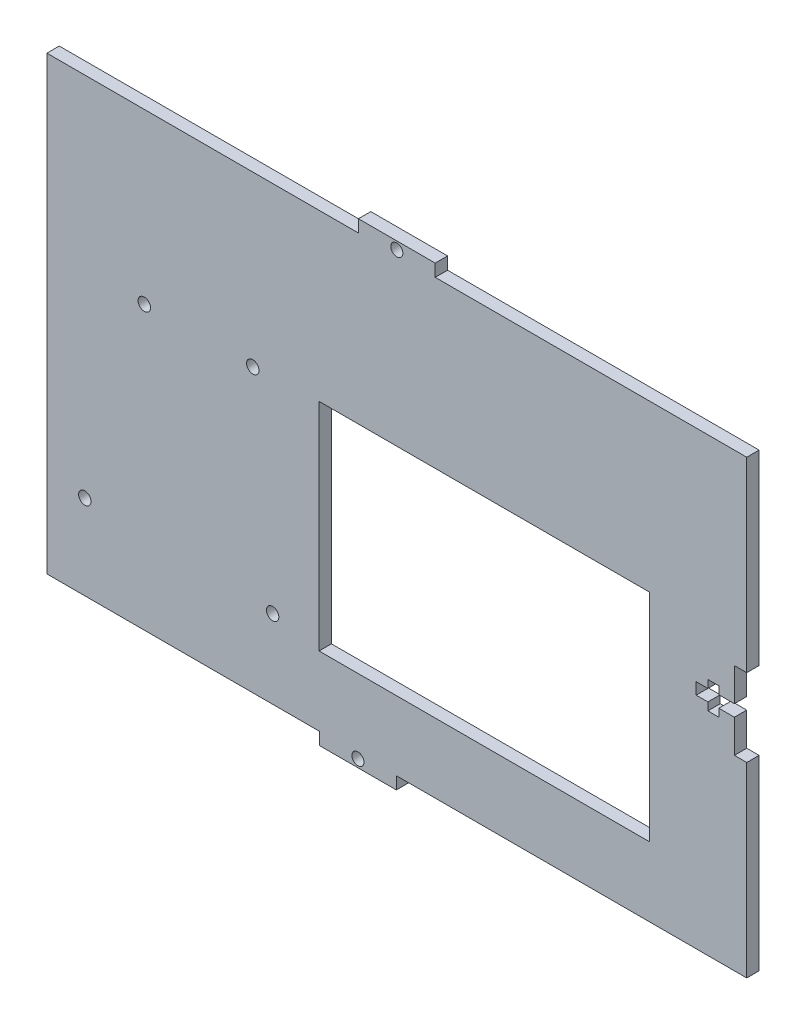
SolidWorks part; units mm, degrees
ref_plane "Front Plane" through (0, 0, 0) normal (0, 0, 1) x (1, 0, 0)
ref_plane "Top Plane" through (0, 0, 0) normal (0, 1, 0) x (1, 0, 0)
ref_plane "Right Plane" through (0, 0, 0) normal (1, 0, 0) x (0, 0, -1)
sketch "Sketch1" plane through (0, 0, 0) normal (0, 0, 1) x (1, 0, 0)
  line L1 (-90, 61.18) -> (90, 61.18)
  line L2 (-90, 61.18) -> (-90, -61.18)
  line L3 (-90, -61.18) -> (90, -61.18)
  line L4 (90, 61.18) -> (90, -61.18)
  dimension "D1" = 61.18
  dimension "D2" = 122.36
  dimension "D3" = 180
  dimension "D4" = 90
extrude "Boss-Extrude1" add sketch "Sketch1" along normal blind 3.18
sketch "Sketch2" plane through (0, 0, 3.18) normal (0, 0, 1) x (1, 0, 0)
  line L0 (0, 0) -> (77, 0) construction
  line L1 (0, 0) -> (0, -50000) construction
  line L4 (90, -61.18) -> (90, 61.18) construction
  line L5 (80, 1.5) -> (77, 1.5)
  line L6 (90, 10) -> (86.82, 10)
  line L7 (90, 10) -> (90, -10)
  line L8 (90, -10) -> (86.82, -10)
  line L9 (86.82, 10) -> (86.82, 1.5)
  line L10 (86.82, 1.5) -> (82.82, 1.5)
  line L12 (86.82, -1.5) -> (82.82, -1.5)
  line L13 (77, 1.5) -> (77, -1.5)
  line L14 (80, 3.5) -> (82.82, 3.5)
  line L15 (80, 3.5) -> (80, 1.5)
  line L16 (80, -3.5) -> (82.82, -3.5)
  line L17 (82.82, 3.5) -> (82.82, 1.5)
  line L18 (80, -1.5) -> (80, -3.5)
  line L19 (90, 0) -> (50000, 0) construction
  line L20 (80, -1.5) -> (77, -1.5)
  line L21 (82.82, -1.5) -> (82.82, -3.5)
  line L22 (86.82, -1.5) -> (86.82, -10)
  dimension "D1" = 3.18
  dimension "D2" = 20
  dimension "D3" = 10
  dimension "D4" = 9.82
  dimension "D5" = 3
  dimension "D6" = 1.5
  dimension "D7" = 2.82
  dimension "D8" = 3.5
  dimension "D9" = 7
  dimension "D10" = 3
extrude "Cut-Extrude1" cut sketch "Sketch2" against normal through all both and the other way through all
sketch "Sketch3" plane through (0, 0, 3.18) normal (0, 0, 1) x (1, 0, 0)
  line L0 (0, 0) -> (50000, 0) construction
  line L1 (0, 0) -> (0, -50000) construction
  line L3 (-90, -61.18) -> (-19.875, -61.18)
  line L4 (-90, -61.18) -> (-90, -58)
  line L5 (-90, -58) -> (-19.875, -58)
  line L6 (-19.875, -61.18) -> (-19.875, -58)
  line L7 (90, -61.18) -> (-0.125, -61.18)
  line L8 (90, -61.18) -> (90, -58)
  line L9 (90, -58) -> (-0.125, -58)
  line L10 (-0.125, -61.18) -> (-0.125, -58)
  dimension "D1" = 70.125
  dimension "D2" = 90.125
  dimension "D3" = 3.18
  dimension "D4" = 3.18
extrude "Cut-Extrude2" cut sketch "Sketch3" against normal through all both and the other way through all
sketch "Sketch4" plane through (0, 0, 3.18) normal (0, 0, 1) x (1, 0, 0)
  line L0 (-19.875, -61.18) -> (-0.125, -61.18) construction
  line L1 (-0.125, -58) -> (-0.125, -61.18) construction
  circle A0 centre (-10, -59.18) radius 1.55
  dimension "D1" = 3.1
  dimension "D2" = 2
  dimension "D3" = 9.875
extrude "Cut-Extrude3" cut sketch "Sketch4" against normal through all both and the other way through all
sketch "Sketch5" plane through (0, 0, 3.18) normal (0, 0, 1) x (1, 0, 0)
  line L0 (-86.82, 58) -> (-86.82, -49942) construction
  line L2 (-90, 61.18) -> (-90, -58) construction
  dimension "D1" = 3.18
sketch "Sketch6" plane through (0, 0, 3.18) normal (0, 0, 1) x (1, 0, 0)
  circle A0 centre (-64.9463, 14.6) radius 1.6
  circle A1 centre (-80.2463, -36.2) radius 1.6
  circle A2 centre (-31.9463, -37.8) radius 1.6
  circle A3 centre (-37.0463, 14.6) radius 1.6
  dimension "D1" = 3.2
  dimension "D2" = 3.2
  dimension "D3" = 3.2
  dimension "D4" = 3.2
extrude "Cut-Extrude4" cut sketch "Sketch6" against normal through all both and the other way through all
sketch "Sketch7" plane through (0, 0, 0) normal (0, 0, -1) x (-1, 0, 0)
  line L0 (-90, -58) -> (0.125, -58) construction
  line L1 (-65, 15.4402) -> (20, 15.4402)
  line L2 (-65, 15.4402) -> (-65, -40.1598)
  line L3 (-65, -40.1598) -> (20, -40.1598)
  line L4 (20, 15.4402) -> (20, -40.1598)
  line L5 (-90, -58) -> (-90, -10) construction
  dimension "D1" = 85
  dimension "D2" = 55.6
  dimension "D3" = 17.8402
  dimension "D4" = 25
extrude "Cut-Extrude5" cut sketch "Sketch7" against normal through all both and the other way through all
sketch "Sketch8" plane through (0, 0, 3.18) normal (0, 0, 1) x (1, 0, 0)
  line L1 (-90, 61.18) -> (-9.875, 61.18)
  line L2 (-90, 61.18) -> (-90, 58)
  line L3 (-90, 58) -> (-9.875, 58)
  line L4 (-9.875, 61.18) -> (-9.875, 58)
  line L5 (90, 61.18) -> (9.875, 61.18)
  line L6 (90, 61.18) -> (90, 58)
  line L7 (90, 58) -> (9.875, 58)
  line L8 (9.875, 61.18) -> (9.875, 58)
  dimension "D1" = 3.18
  dimension "D2" = 80.125
  dimension "D3" = 3.18
  dimension "D4" = 80.125
extrude "Cut-Extrude6" cut sketch "Sketch8" against normal through all both and the other way through all
sketch "Sketch9" plane through (0, 0, 3.18) normal (0, 0, 1) x (1, 0, 0)
  line L0 (9.875, 61.18) -> (9.875, 58) construction
  line L1 (9.875, 61.18) -> (-9.875, 61.18) construction
  circle A0 centre (0, 59.18) radius 1.55
  point P4 (9.875, 59.59)
  dimension "D1" = 3.1
  dimension "D2" = 9.875
  dimension "D3" = 2
extrude "Cut-Extrude7" cut sketch "Sketch9" against normal through all both and the other way through all
